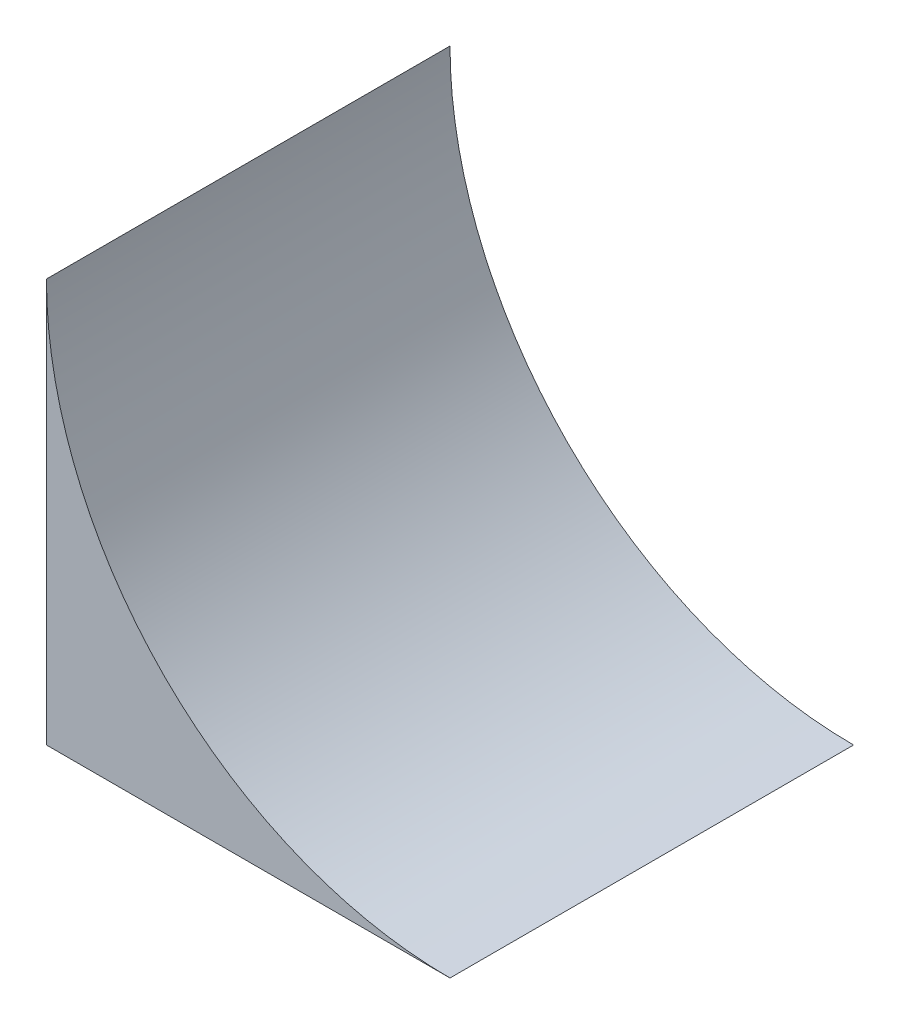
SolidWorks part; units mm, degrees
ref_plane "Alzado" through (0, 0, 0) normal (0, 0, 1) x (1, 0, 0)
ref_plane "Planta" through (0, 0, 0) normal (0, 1, 0) x (1, 0, 0)
ref_plane "Vista lateral" through (0, 0, 0) normal (1, 0, 0) x (0, 0, -1)
sketch "Croquis1" plane through (0, 0, 0) normal (0, 0, 1) x (1, 0, 0)
  line L1 (0, 0) -> (6, 0)
  line L2 (0, 0) -> (0, 6)
  arc A0 (0, 6) -> (6, 0) centre (6, 6) ccw
  dimension "D1" = 12
extrude "Saliente-Extruir1" add sketch "Croquis1" along normal blind 6
